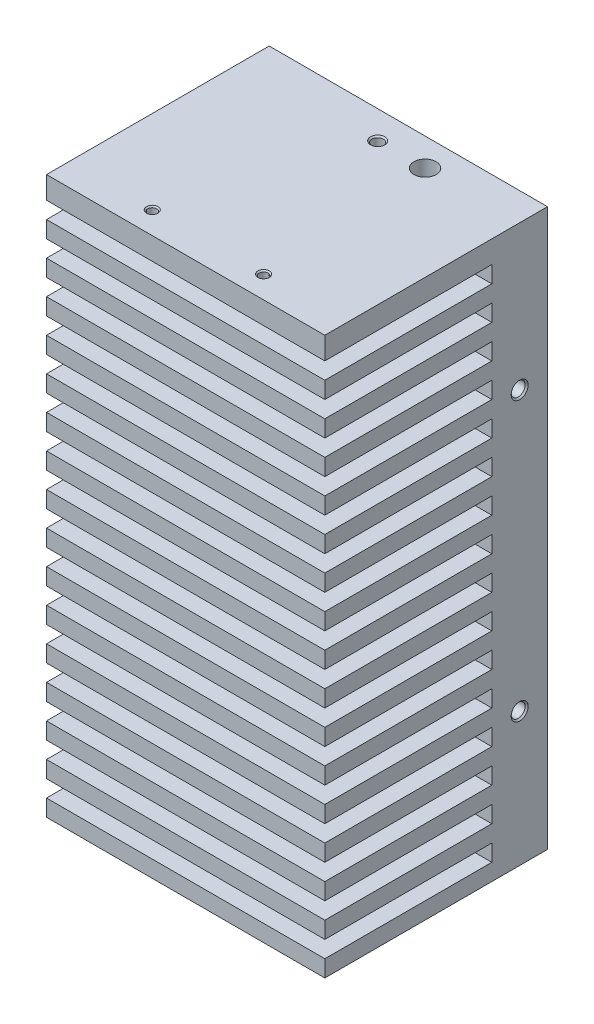
SolidWorks part; units mm, degrees
material "aluminum"
ref_plane "Front Plane" through (0, 0, 0) normal (0, 0, 1) x (1, 0, 0)
ref_plane "Top Plane" through (0, 0, 0) normal (0, 1, 0) x (1, 0, 0)
ref_plane "Right Plane" through (0, 0, 0) normal (1, 0, 0) x (0, 0, -1)
sketch "Sketch2" plane through (0, 0, 0) normal (0, 0, 1) x (1, 0, 0)
  line L1 (0, 0) -> (50, 0)
  line L2 (0, 0) -> (0, 100)
  line L3 (0, 100) -> (50, 100)
  line L4 (50, 0) -> (50, 100)
  dimension "D1" = 50
  dimension "D2" = 100
extrude "Boss-Extrude1" add sketch "Sketch2" along normal blind 40
sketch "Sketch3" plane through (50, 0, 0) normal (1, 0, 0) x (0, 0, -1)
  line L0 (-40, 100) -> (0, 100) construction
  line L1 (0, 0) -> (0, 100) construction
  circle A0 centre (-5, 74) radius 1.25
  circle A1 centre (-5, 24) radius 1.25
  dimension "D1" = 2.5
  dimension "D2" = 26
  dimension "D4" = 5
  dimension "D3" = 76
hole_wizard "M3 Tapped Hole2" positions "Sketch21" profile "Sketch22" tap size "M3" standard "ISO"
sketch "Sketch21" plane through (50, 0, 0) normal (1, 0, 0) x (0, 0, -1)
  point P0 (-5, 74)
  point P3 (-5, 24)
sketch "Sketch22" plane through (50, 74, 5) normal (0, 1, 0) x (0, 0, -1)
  line L0 (0, 0) -> (0, 10.7511)
  line L1 (0, 10.7511) -> (1.25, 10)
  line L2 (1.25, 10) -> (1.25, 0.275)
  line L3 (1.25, 0.275) -> (1.525, 0)
  line L5 (1.525, 0) -> (0, 0)
  line L6 (-1.25, 0.275) -> (-1.525, 0) construction
  line L10 (0, 10.7511) -> (-1.25, 10) construction
  line L11 (0, -6.35) -> (0, 107.95) construction
  dimension "Tap Drill Dia." = 2.5
  dimension "Tap Drill Depth" = 10
  dimension "Near C'Sink Dia." = 3.05
  dimension "Near C'Sink Angle" = 90
  dimension "Drill Angle" = 118
cosmetic thread "Hole Thread8" parameters "D1"=6, "D2"=3
cosmetic thread "Hole Thread9" parameters "D1"=6, "D2"=3
sketch "Sketch5" plane through (0, 0, 0) normal (0, 0, 1) x (1, 0, 0)
  line L0 (20, 0) -> (20, 100) construction
  line L1 (0, 0) -> (50, 0) construction
  line L2 (50, 100) -> (0, 100) construction
  line L3 (0, 100) -> (0, 0) construction
  line L5 (50, 0) -> (50, 100) construction
  line L6 (50, 24) -> (0, 24) construction
  line L7 (0, 100) -> (0, 0) construction
  line L9 (14.8, 14.75) -> (26.8, 14.75)
  line L10 (14.8, 14.75) -> (14.8, 25.25)
  line L11 (14.8, 25.25) -> (26.8, 25.25)
  line L12 (26.8, 14.75) -> (26.8, 25.25)
  line L13 (14.8, 14.75) -> (26.8, 25.25) construction
  line L14 (14.8, 25.25) -> (26.8, 14.75) construction
  circle A5 centre (26.8, 25.25) radius 0.8
  circle A7 centre (14.8, 14.75) radius 0.8
  point P13 (20.8, 20)
  point P15 (20.8, 20)
  dimension "D6" = 10.5
  dimension "D7" = 1.6
  dimension "D1" = 20
  dimension "D2" = 76
  dimension "D3" = 4
  dimension "D4" = 0.8
  dimension "D5" = 12
hole_wizard "M2 Tapped Hole1" positions "Sketch11" profile "Sketch12" tap size "M2" standard "ISO"
sketch "Sketch11" plane through (0, 0, 0) normal (0, 0, -1) x (-1, 0, 0)
  point P0 (-26.8, 25.25)
  point P3 (-14.8, 14.75)
sketch "Sketch12" plane through (26.8, 25.25, 0) normal (1, 0, 0) x (0, 1, 0)
  line L0 (0, 0) -> (0, 10.4807)
  line L1 (0, 10.4807) -> (0.8, 10)
  line L2 (0.8, 10) -> (0.8, 0.225)
  line L3 (0.8, 0.225) -> (1.025, 0)
  line L5 (1.025, 0) -> (0, 0)
  line L6 (-0.8, 0.225) -> (-1.025, 0) construction
  line L10 (0, 10.4807) -> (-0.8, 10) construction
  line L11 (0, -6.35) -> (0, 107.95) construction
  dimension "Tap Drill Dia." = 1.6
  dimension "Tap Drill Depth" = 10
  dimension "Near C'Sink Dia." = 2.05
  dimension "Near C'Sink Angle" = 90
  dimension "Drill Angle" = 118
cosmetic thread "Hole Thread1" parameters "D1"=4, "D2"=2
cosmetic thread "Hole Thread2" parameters "D1"=4, "D2"=2
pattern_linear "LPattern1" count 3 spacing 30 of "M2 Tapped Hole1"
sketch "Sketch6" plane through (0, 100, 0) normal (0, 1, 0) x (1, 0, 0)
  line L2 (0, -40) -> (0, 0) construction
  line L3 (50, 0) -> (0, 0) construction
  circle A0 centre (33, -5) radius 2
  dimension "D1" = 4
  dimension "D2" = 5
  dimension "D3" = 33
extrude "Cut-Extrude4" cut sketch "Sketch6" against normal blind 25
sketch "Sketch7" plane through (0, 100, 0) normal (0, 1, 0) x (1, 0, 0)
  line L2 (50, -40) -> (50, 0) construction
  circle A0 centre (24.5, -5) radius 1.25
  point P4 (33, -5)
  dimension "D1" = 2.5
  dimension "D2" = 25.5
hole_wizard "M2.5 Tapped Hole1" positions "Sketch13" profile "Sketch14" tap size "M2.5" standard "ISO"
sketch "Sketch13" plane through (0, 100, 0) normal (0, 1, 0) x (1, 0, 0)
  point P0 (24.5, -5)
sketch "Sketch14" plane through (24.5, 100, 5) normal (1, 0, 0) x (0, 0, 1)
  line L0 (0, 0) -> (0, 10.6159)
  line L1 (0, 10.6159) -> (1.025, 10)
  line L2 (1.025, 10) -> (1.025, 0.25)
  line L3 (1.025, 0.25) -> (1.275, 0)
  line L5 (1.275, 0) -> (0, 0)
  line L6 (-1.025, 0.25) -> (-1.275, 0) construction
  line L10 (0, 10.6159) -> (-1.025, 10) construction
  line L11 (0, -6.35) -> (0, 107.95) construction
  dimension "Tap Drill Dia." = 2.05
  dimension "Tap Drill Depth" = 10
  dimension "Near C'Sink Dia." = 2.55
  dimension "Near C'Sink Angle" = 90
  dimension "Drill Angle" = 118
cosmetic thread "Hole Thread3" parameters "D1"=5, "D2"=2.5
sketch "Sketch8" plane through (50, 0, 0) normal (1, 0, 0) x (0, 0, -1)
  line L0 (-40, 0) -> (-40, 100) construction
  line L1 (-40, 3) -> (-10, 3)
  line L2 (-40, 3) -> (-40, 6)
  line L3 (-40, 6) -> (-10, 6)
  line L4 (-10, 3) -> (-10, 6)
  line L5 (0, 0) -> (0, 100) construction
  line L6 (-40, 0) -> (0, 0) construction
  line L7 (-40, 9) -> (-40, 12)
  line L8 (-40, 9) -> (-10, 9)
  line L9 (-10, 9) -> (-10, 12)
  line L10 (-40, 12) -> (-10, 12)
  line L11 (-40, 15) -> (-40, 18)
  line L12 (-40, 15) -> (-10, 15)
  line L13 (-10, 15) -> (-10, 18)
  line L14 (-40, 18) -> (-10, 18)
  line L15 (-40, 21) -> (-40, 24)
  line L16 (-40, 21) -> (-10, 21)
  line L17 (-10, 21) -> (-10, 24)
  line L18 (-40, 24) -> (-10, 24)
  line L19 (-40, 27) -> (-40, 30)
  line L20 (-40, 27) -> (-10, 27)
  line L21 (-10, 27) -> (-10, 30)
  line L22 (-40, 30) -> (-10, 30)
  line L23 (-40, 33) -> (-40, 36)
  line L24 (-40, 33) -> (-10, 33)
  line L25 (-10, 33) -> (-10, 36)
  line L26 (-40, 36) -> (-10, 36)
  line L27 (-40, 39) -> (-40, 42)
  line L28 (-40, 39) -> (-10, 39)
  line L29 (-10, 39) -> (-10, 42)
  line L30 (-40, 42) -> (-10, 42)
  line L31 (-40, 45) -> (-40, 48)
  line L32 (-40, 45) -> (-10, 45)
  line L33 (-10, 45) -> (-10, 48)
  line L34 (-40, 48) -> (-10, 48)
  line L35 (-40, 51) -> (-40, 54)
  line L36 (-40, 51) -> (-10, 51)
  line L37 (-10, 51) -> (-10, 54)
  line L38 (-40, 54) -> (-10, 54)
  line L39 (-40, 57) -> (-40, 60)
  line L40 (-40, 57) -> (-10, 57)
  line L41 (-10, 57) -> (-10, 60)
  line L42 (-40, 60) -> (-10, 60)
  line L43 (-40, 63) -> (-40, 66)
  line L44 (-40, 63) -> (-10, 63)
  line L45 (-10, 63) -> (-10, 66)
  line L46 (-40, 66) -> (-10, 66)
  line L47 (-40, 69) -> (-40, 72)
  line L48 (-40, 69) -> (-10, 69)
  line L49 (-10, 69) -> (-10, 72)
  line L50 (-40, 72) -> (-10, 72)
  line L51 (-40, 75) -> (-40, 78)
  line L52 (-40, 75) -> (-10, 75)
  line L53 (-10, 75) -> (-10, 78)
  line L54 (-40, 78) -> (-10, 78)
  line L55 (-40, 81) -> (-40, 84)
  line L56 (-40, 81) -> (-10, 81)
  line L57 (-10, 81) -> (-10, 84)
  line L58 (-40, 84) -> (-10, 84)
  line L59 (-40, 87) -> (-40, 90)
  line L60 (-40, 87) -> (-10, 87)
  line L61 (-10, 87) -> (-10, 90)
  line L62 (-40, 90) -> (-10, 90)
  line L63 (-40, 93) -> (-40, 96)
  line L64 (-40, 93) -> (-10, 93)
  line L65 (-10, 93) -> (-10, 96)
  line L66 (-40, 96) -> (-10, 96)
  dimension "D1" = 10
  dimension "D2" = 3
  dimension "D3" = 3
  dimension "D4" = 16
extrude "Cut-Extrude6" cut sketch "Sketch8" against normal through all
sketch "Sketch9" plane through (0, 100, 0) normal (0, 1, 0) x (1, 0, 0)
  line L0 (0, -36) -> (50, -36) construction
  line L1 (0, -40) -> (0, 0) construction
  line L2 (50, -40) -> (50, 0) construction
  line L3 (50, -40) -> (0, -40) construction
  circle A0 centre (15, -36) radius 0.85
  circle A1 centre (35, -36) radius 0.85
  point P8 (25, -36)
  dimension "D2" = 10
  dimension "D4" = 1.7
  dimension "D1" = 4
  dimension "D3" = 10
hole_wizard "M2 Tapped Hole2" positions "Sketch17" profile "Sketch18" tap size "M2" standard "ISO"
sketch "Sketch17" plane through (0, 100, 0) normal (0, 1, 0) x (1, 0, 0)
  point P0 (15, -36)
  point P3 (35, -36)
sketch "Sketch18" plane through (15, 100, 36) normal (1, 0, 0) x (0, 0, 1)
  line L0 (0, 0) -> (0, 10.4807)
  line L1 (0, 10.4807) -> (0.8, 10)
  line L2 (0.8, 10) -> (0.8, 0.225)
  line L3 (0.8, 0.225) -> (1.025, 0)
  line L5 (1.025, 0) -> (0, 0)
  line L6 (-0.8, 0.225) -> (-1.025, 0) construction
  line L10 (0, 10.4807) -> (-0.8, 10) construction
  line L11 (0, -6.35) -> (0, 107.95) construction
  dimension "Tap Drill Dia." = 1.6
  dimension "Tap Drill Depth" = 10
  dimension "Near C'Sink Dia." = 2.05
  dimension "Near C'Sink Angle" = 90
  dimension "Drill Angle" = 118
cosmetic thread "Hole Thread4" parameters "D1"=4, "D2"=2
cosmetic thread "Hole Thread5" parameters "D1"=4, "D2"=2
sketch "Sketch10" plane through (0, 0, 0) normal (0, -1, 0) x (1, 0, 0)
  line L0 (50, 36) -> (0, 36)
  line L1 (50, 40) -> (50, 0) construction
  line L2 (0, 40) -> (0, 0) construction
  line L3 (0, 40) -> (50, 40) construction
  circle A0 centre (35, 36) radius 0.85
  circle A1 centre (15, 36) radius 0.85
  point P8 (25, 36)
  dimension "D2" = 1.7
  dimension "D1" = 4
  dimension "D3" = 10
  dimension "D4" = 10
hole_wizard "M2 Tapped Hole3" positions "Sketch19" profile "Sketch20" tap size "M2" standard "ISO"
sketch "Sketch19" plane through (0, 0, 0) normal (0, -1, 0) x (-1, 0, 0)
  point P0 (-15, -36)
  point P3 (-35, -36)
sketch "Sketch20" plane through (15, 0, 36) normal (1, 0, 0) x (0, 0, -1)
  line L0 (0, 0) -> (0, 10.4807)
  line L1 (0, 10.4807) -> (0.8, 10)
  line L2 (0.8, 10) -> (0.8, 0.225)
  line L3 (0.8, 0.225) -> (1.025, 0)
  line L5 (1.025, 0) -> (0, 0)
  line L6 (-0.8, 0.225) -> (-1.025, 0) construction
  line L10 (0, 10.4807) -> (-0.8, 10) construction
  line L11 (0, -6.35) -> (0, 107.95) construction
  dimension "Tap Drill Dia." = 1.6
  dimension "Tap Drill Depth" = 10
  dimension "Near C'Sink Dia." = 2.05
  dimension "Near C'Sink Angle" = 90
  dimension "Drill Angle" = 118
cosmetic thread "Hole Thread6" parameters "D1"=4, "D2"=2
cosmetic thread "Hole Thread7" parameters "D1"=4, "D2"=2
